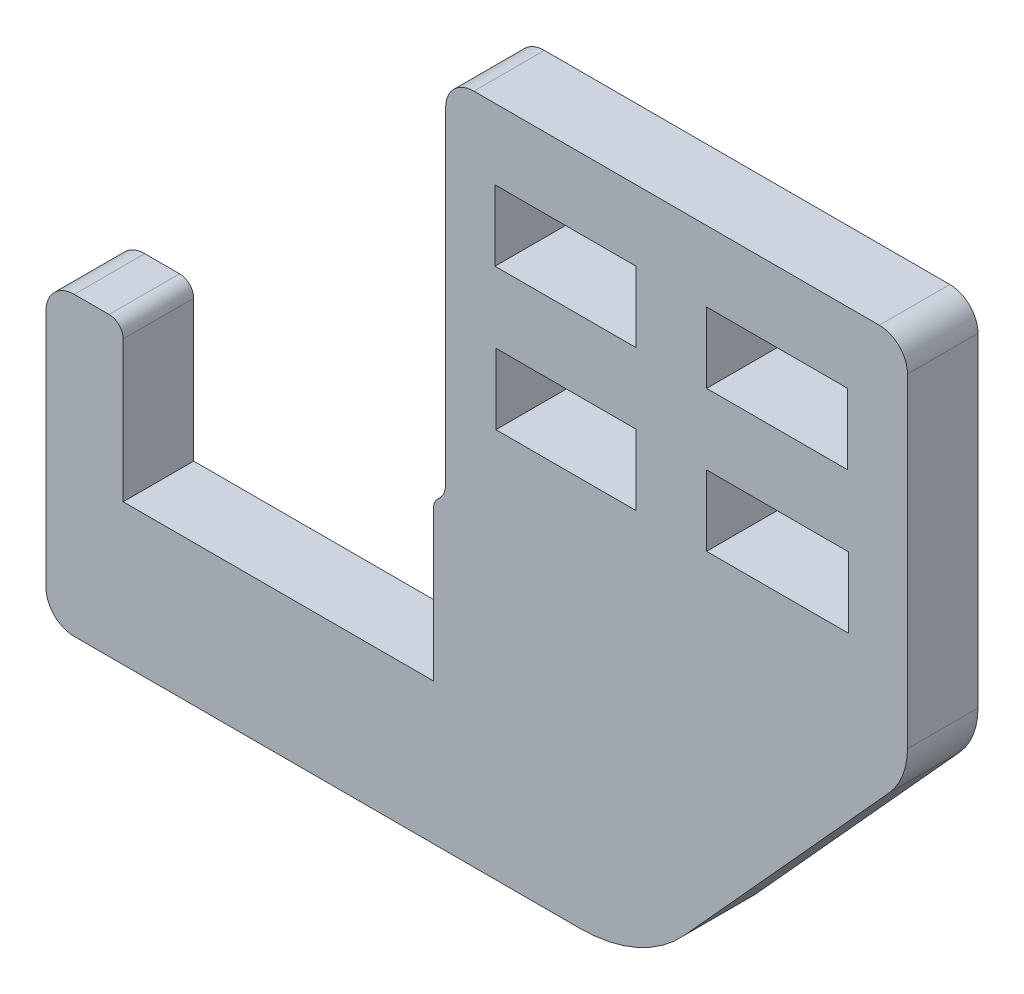
SolidWorks part; units mm, degrees
ref_plane "Front Plane" through (0, 0, 0) normal (0, 0, 1) x (1, 0, 0)
ref_plane "Top Plane" through (0, 0, 0) normal (0, 1, 0) x (1, 0, 0)
ref_plane "Right Plane" through (0, 0, 0) normal (1, 0, 0) x (0, 0, -1)
sketch "Sketch1" plane through (0, 0, 0) normal (0, 0, 1) x (1, 0, 0)
  line L0 (45, 7.5) -> (45, 30.5)
  line L1 (12.2604, 7.3562) -> (12.2604, 30.5)
  line L2 (-14.0707, -15.1438) -> (21.7819, -15.1438)
  line L3 (11.4004, 5.4693) -> (11.4004, -5.1438)
  line L4 (15.7604, 27.5) -> (25.7604, 27.5)
  line L5 (14.2604, 32.5) -> (43, 32.5)
  line L6 (15.8244, 17.4955) -> (25.7604, 17.4955)
  line L7 (15.7604, 27.5) -> (15.7604, 22.5)
  line L8 (15.7604, 22.5) -> (25.7604, 22.5)
  line L9 (25.7604, 27.5) -> (25.7604, 22.5)
  line L10 (30.7604, 27.5) -> (40.7604, 27.5)
  line L11 (30.7604, 27.5) -> (30.7604, 22.5)
  line L12 (30.7604, 22.5) -> (40.7604, 22.5)
  line L13 (40.7604, 27.5) -> (40.7604, 22.5)
  line L14 (-14.0707, 5.8562) -> (-11.5996, 5.8562)
  line L15 (11.4004, -5.1438) -> (-10.5996, -5.1438)
  line L16 (43.7036, 4.1409) -> (29.189, -11.862)
  line L17 (-16.0707, 3.8562) -> (-16.0707, -13.1438)
  line L18 (-10.5996, -5.1438) -> (-10.5996, 4.8562)
  line L19 (15.8244, 17.4955) -> (15.8244, 12.4955)
  line L20 (15.8244, 12.4955) -> (25.7604, 12.4955)
  line L21 (25.7604, 17.4955) -> (25.7604, 12.4955)
  line L22 (30.7604, 17.4955) -> (40.8244, 17.4955)
  line L23 (30.7604, 17.4955) -> (30.7604, 12.4955)
  line L24 (30.7604, 12.4955) -> (40.8244, 12.4955)
  line L25 (40.8244, 17.4955) -> (40.8244, 12.4955)
  arc A0 (29.189, -11.862) -> (21.7819, -15.1438) centre (21.7819, -5.1438) cw
  arc A1 (-16.0707, -13.1438) -> (-14.0707, -15.1438) centre (-14.0707, -13.1438) ccw
  arc A2 (12.2604, 7.3562) -> (11.7444, 6.2241) centre (10.7604, 7.3562) cw
  arc A3 (12.2604, 30.5) -> (14.2604, 32.5) centre (14.2604, 30.5) cw
  arc A4 (45, 30.5) -> (43, 32.5) centre (43, 30.5) ccw
  arc A5 (-14.0707, 5.8562) -> (-16.0707, 3.8562) centre (-14.0707, 3.8562) ccw
  arc A6 (45, 7.5) -> (43.7036, 4.1409) centre (40, 7.5) cw
  arc A7 (11.4004, 5.4693) -> (11.7444, 6.2241) centre (12.4004, 5.4693) cw
  arc A8 (-10.5996, 4.8562) -> (-11.5996, 5.8562) centre (-11.5996, 4.8562) ccw
  dimension "D2" = 1.5
  dimension "D3" = 2
  dimension "D4" = 2
  dimension "D9" = 10
  dimension "D12" = 5
  dimension "D13" = 2
  dimension "D10" = 2
  dimension "D7" = 1
  dimension "D14" = 1
  dimension "D5" = 5
  dimension "D6" = 10
  dimension "D8" = 5
  dimension "D11" = 5
  dimension "D15" = 5
extrude "Boss-Extrude1" add sketch "Sketch1" along normal blind 5
